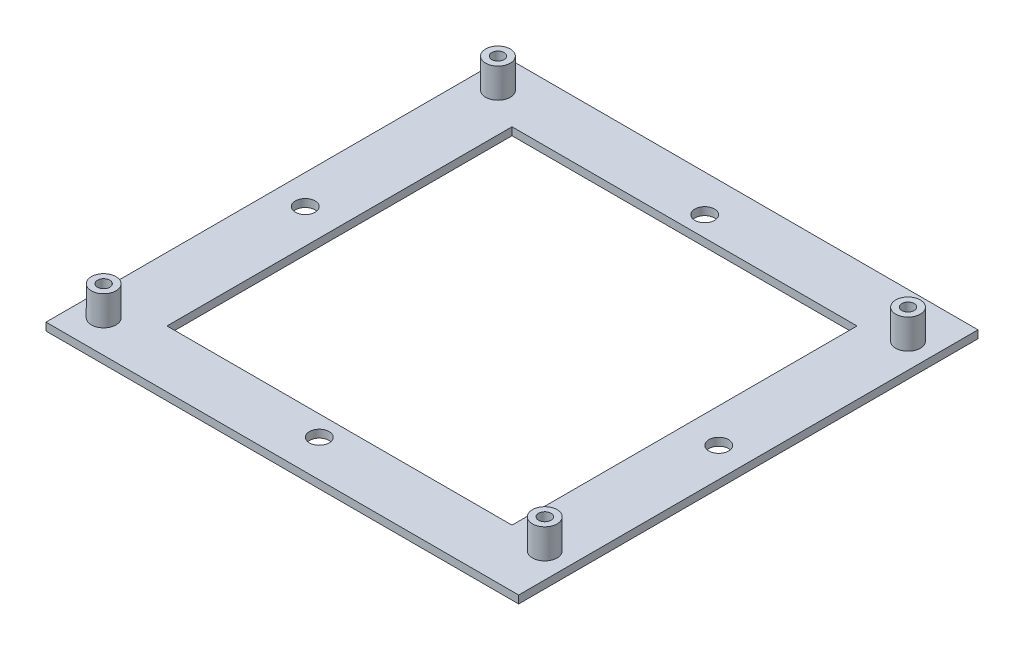
SolidWorks part; units mm, degrees
material "5052-H36"
ref_plane "Front Plane" through (0, 0, 0) normal (0, 0, 1) x (1, 0, 0)
ref_plane "Top Plane" through (0, 0, 0) normal (0, 1, 0) x (1, 0, 0)
ref_plane "Right Plane" through (0, 0, 0) normal (1, 0, 0) x (0, 0, -1)
sketch "Sketch2" plane through (0, 0, 0) normal (0, 1, 0) x (1, 0, 0)
  line L0 (-41.95, 0) -> (41.95, 0) construction
  line L1 (-47.95, -46.6) -> (47.95, -46.6)
  line L2 (-47.95, -46.6) -> (-47.95, 46.6)
  line L3 (-47.95, 46.6) -> (47.95, 46.6)
  line L4 (47.95, -46.6) -> (47.95, 46.6)
  line L5 (-47.95, -46.6) -> (47.95, 46.6) construction
  line L6 (-47.95, 46.6) -> (47.95, -46.6) construction
  line L7 (-35, -35) -> (35, -35)
  line L8 (-35, -35) -> (-35, 35)
  line L9 (-35, 35) -> (35, 35)
  line L10 (35, -35) -> (35, 35)
  line L11 (-35, -35) -> (35, 35) construction
  line L12 (-35, 35) -> (35, -35) construction
  line L13 (0, -39.1) -> (0, 39.1) construction
  circle A0 centre (0, 39.1) radius 2
  circle A1 centre (41.95, 0) radius 2
  circle A2 centre (-41.95, 0) radius 2
  circle A3 centre (0, -39.1) radius 2
  point P0 (0, 0)
  point P6 (0, 0)
  point P11 (42.85, 37.5)
  point P12 (42.85, -36.2)
  point P13 (-42.85, 40)
  point P14 (-42.85, -40)
  point P18 (0, 0)
  point P21 (0, 0)
extrude "Boss-Extrude1" add sketch "Sketch2" along normal blind 1.58
sketch "Sketch3" plane through (0, 1.58, 0) normal (0, 1, 0) x (1, 0, 0)
  circle A0 centre (-42.85, 40) radius 2.5
  circle A1 centre (42.85, 37.5) radius 2.5
  circle A2 centre (-42.85, -40) radius 2.5
  circle A3 centre (42.85, -36.2) radius 2.5
  point P0 (42.85, -36.2)
  point P1 (42.85, 37.5)
  point P2 (-42.85, 40)
  point P3 (-42.85, -40)
extrude "Boss-Extrude2" add sketch "Sketch3" along normal blind 6
hole_wizard "M3x0.5 Tapped Hole1" positions "3DSketch1" profile "Sketch4" tap size "M3x0.5" standard "ANSI Metric"
sketch3d "3DSketch1"
  line L0 (-42.85, 7.58, -40) -> (-42.85, 1.58, -40) construction
  line L1 (-42.85, 7.58, 40) -> (-42.85, 1.58, 40) construction
  line L2 (42.85, 7.58, 36.2) -> (42.85, 1.58, 36.2) construction
  line L3 (42.85, 7.58, -37.5) -> (42.85, 1.58, -37.5) construction
  point P0 (-42.85, 7.58, -40)
  point P4 (-42.85, 7.58, 40)
  point P8 (42.85, 7.58, 36.2)
  point P12 (42.85, 7.58, -37.5)
sketch "Sketch4" plane through (-42.85, 7.58, -40) normal (1, 0, 0) x (0, 0, 1)
  line L0 (0, 0) -> (0, 6.7511)
  line L1 (0, 6.7511) -> (1.25, 6)
  line L2 (1.25, 6) -> (1.25, 0)
  line L5 (1.25, 0) -> (0, 0)
  line L10 (0, 6.7511) -> (-1.25, 6) construction
  line L11 (0, -6.35) -> (0, 107.95) construction
  dimension "Tap Drill Dia." = 2.5
  dimension "Tap Drill Depth" = 6
  dimension "Drill Angle" = 118
cosmetic thread "Hole Thread1" parameters "D1"=6, "D2"=3
cosmetic thread "Hole Thread2" parameters "D1"=6, "D2"=3
cosmetic thread "Hole Thread3" parameters "D1"=6, "D2"=3
cosmetic thread "Hole Thread4" parameters "D1"=6, "D2"=3
